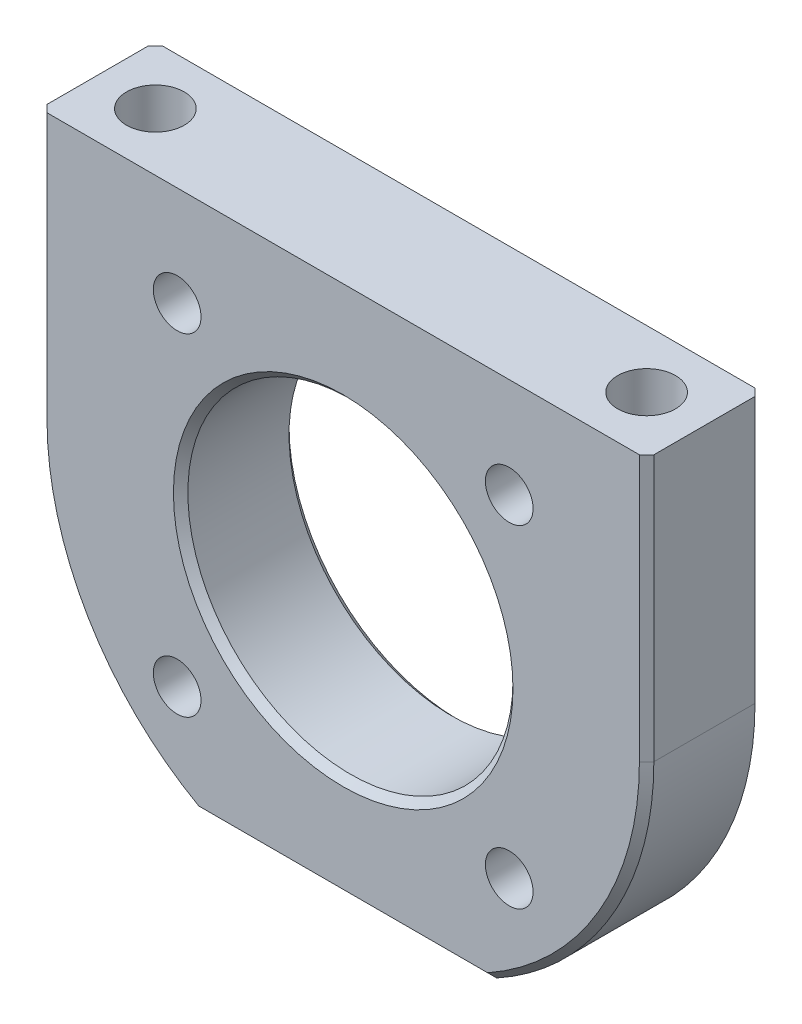
SolidWorks part; units mm, degrees
ref_plane "Front Plane" through (0, 0, 0) normal (0, 0, 1) x (1, 0, 0)
ref_plane "Top Plane" through (0, 0, 0) normal (0, 1, 0) x (1, 0, 0)
ref_plane "Right Plane" through (0, 0, 0) normal (1, 0, 0) x (0, 0, -1)
sketch "Sketch1" plane through (0, 0, 0) normal (0, 0, 1) x (1, 0, 0)
  line L0 (21, 0) -> (21, 18.4)
  line L3 (-10.1213, -18.4) -> (10.1213, -18.4)
  line L4 (-21, 0) -> (-21, 18.4)
  line L5 (-21, 18.4) -> (21, 18.4)
  arc A0 (10.1213, -18.4) -> (21, 0) centre (0, 0) ccw
  arc A1 (-21, 0) -> (-10.1213, -18.4) centre (0, 0) ccw
  dimension "D1" = 21
  dimension "D4" = 21
  dimension "D2" = 21
  dimension "D3" = 18.4
  dimension "D5" = 36.8
extrude "Boss-Extrude1" add sketch "Sketch1" along normal mid plane 8
sketch "Sketch2" plane through (0, 0, 4) normal (0, 0, 1) x (1, 0, 0)
  circle A0 centre (0, 0) radius 11.25
  dimension "D1" = 22.5
extrude "Cut-Extrude1" cut sketch "Sketch2" against normal through all
hole_wizard "M4x0.7 Tapped Hole3" positions "Sketch12" profile "Sketch11" tap size "M4x0.7" standard "ANSI Metric" end condition through all
sketch "Sketch12" plane through (0, 0, 4) normal (0, 0, 1) x (1, 0, 0)
  line L0 (-1000, 0) -> (49000, 0) construction
  line L1 (-707.1068, -707.1068) -> (34648.2323, 34648.2323) construction
  line L2 (-707.1068, 707.1068) -> (34648.2323, -34648.2323) construction
  circle A0 centre (0, 0) radius 16.25 construction
  point P0 (-11.4905, 11.4905)
  point P2 (11.4905, 11.4905)
  point P4 (11.4905, -11.4905)
  point P6 (-11.4905, -11.4905)
  dimension "D1" = 32.5
  dimension "D2" = 45
  dimension "D3" = 90
sketch "Sketch11" plane through (-11.4905, 11.4905, 4) normal (1, 0, 0) x (0, -1, 0)
  line L0 (0, 0) -> (0, 8)
  line L1 (0, 8) -> (1.65, 8)
  line L2 (1.65, 8) -> (1.65, 0)
  line L5 (1.65, 0) -> (0, 0)
  line L11 (0, -6.35) -> (0, 107.95) construction
  dimension "Thru Tap Drill Dia." = 3.3
  dimension "Thru Tap Drill Depth" = 8
cosmetic thread "Hole Thread7" parameters "D2"=4
cosmetic thread "Hole Thread8" parameters "D2"=4
cosmetic thread "Hole Thread9" parameters "D2"=4
cosmetic thread "Hole Thread10" parameters "D2"=4
hole_wizard "M4x0.7 Tapped Hole1" positions "Sketch8" profile "Sketch7" tap size "M4x0.7" standard "ANSI Metric"
sketch "Sketch8" plane through (0, 18.4, 0) normal (0, 1, 0) x (1, 0, 0)
  line L0 (-1000, 0) -> (49000, 0) construction
  point P0 (-17, 0)
  point P2 (17, 0)
  dimension "D1" = 17
  dimension "D2" = 17
cosmetic thread "Hole Thread1" parameters "D1"=7.3, "D2"=4
cosmetic thread "Hole Thread2" parameters "D1"=7.3, "D2"=4
sketch "Sketch7" plane through (-17, 18.4, 0) normal (1, 0, 0) x (0, 0, 1)
  line L0 (0, 0) -> (0, 8.9914)
  line L1 (0, 8.9914) -> (1.65, 8)
  line L2 (1.65, 8) -> (1.65, 0)
  line L5 (1.65, 0) -> (0, 0)
  line L10 (0, 8.9914) -> (-1.65, 8) construction
  line L11 (0, -6.35) -> (0, 107.95) construction
  dimension "Tap Drill Dia." = 3.3
  dimension "Tap Drill Depth" = 8
  dimension "Drill Angle" = 118
sketch "Sketch6" plane through (-3.375, 18.4, 0) normal (0, -1, 0) x (0, 0, -1)
  line L0 (0, -996.625) -> (0, 49003.375) construction
  circle A0 centre (0, -13.625) radius 2
  circle A1 centre (0, 20.375) radius 2
  dimension "D1" = 17
  dimension "D2" = 17
  dimension "D3" = 4
  dimension "D4" = 4
extrude "Cut-Extrude3" cut sketch "Sketch6" along normal blind 8
chamfer "Chamfer1" distance 0.5 angle 45 16 edges at (11.25, 0, -4) (21, 18.4, 0) (-21, 9.2, 4) (-18.0769, -10.6877, 4) (0, -18.4, 4) (18.0769, -10.6877, 4) (21, 9.2, 4) (0, 18.4, 4) (-21, 18.4, 0) (-21, 9.2, -4) (-18.0769, -10.6877, -4) (0, -18.4, -4) (18.0769, -10.6877, -4) (21, 9.2, -4) (0, 18.4, -4) (11.25, 0, 4)
equation "\"D1@Sketch6\"=34/2"
equation "\"D4@Sketch6\"=\"D3@Sketch6\""
equation "\"D3@Sketch1\"=\"D5@Sketch1\"/2"
equation "\"D2@Sketch6\"=\"D1@Sketch6\""
